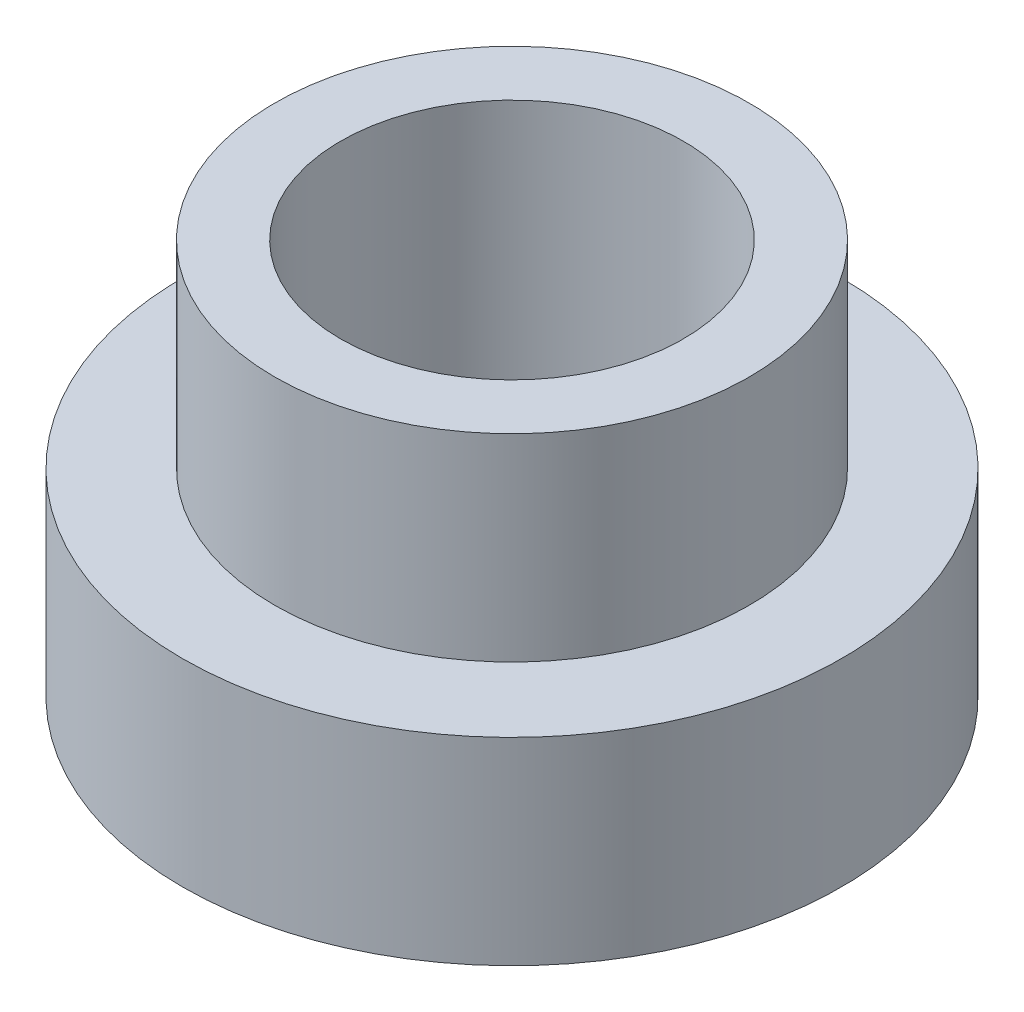
SolidWorks part; units mm, degrees
ref_plane "Front Plane" through (0, 0, 0) normal (0, 0, 1) x (1, 0, 0)
ref_plane "Top Plane" through (0, 0, 0) normal (0, 1, 0) x (1, 0, 0)
ref_plane "Right Plane" through (0, 0, 0) normal (1, 0, 0) x (0, 0, -1)
sketch "Sketch1" plane through (0, 0, 0) normal (0, 1, 0) x (1, 0, 0)
  circle A0 centre (0, 0) radius 5
  dimension "D1" = 10
extrude "Boss-Extrude1" add sketch "Sketch1" along normal blind 3
sketch "Sketch2" plane through (0, 3, 0) normal (0, 1, 0) x (1, 0, 0)
  circle A0 centre (0, 0) radius 3.6
  dimension "D1" = 7.2
extrude "Boss-Extrude2" add sketch "Sketch2" along normal blind 3
sketch "Sketch3" plane through (0, 0, 0) normal (0, 1, 0) x (1, 0, 0)
  circle A0 centre (0, 0) radius 2.6
  dimension "D1" = 5.2
extrude "Cut-Extrude1" cut sketch "Sketch3" along normal through all contours A0
